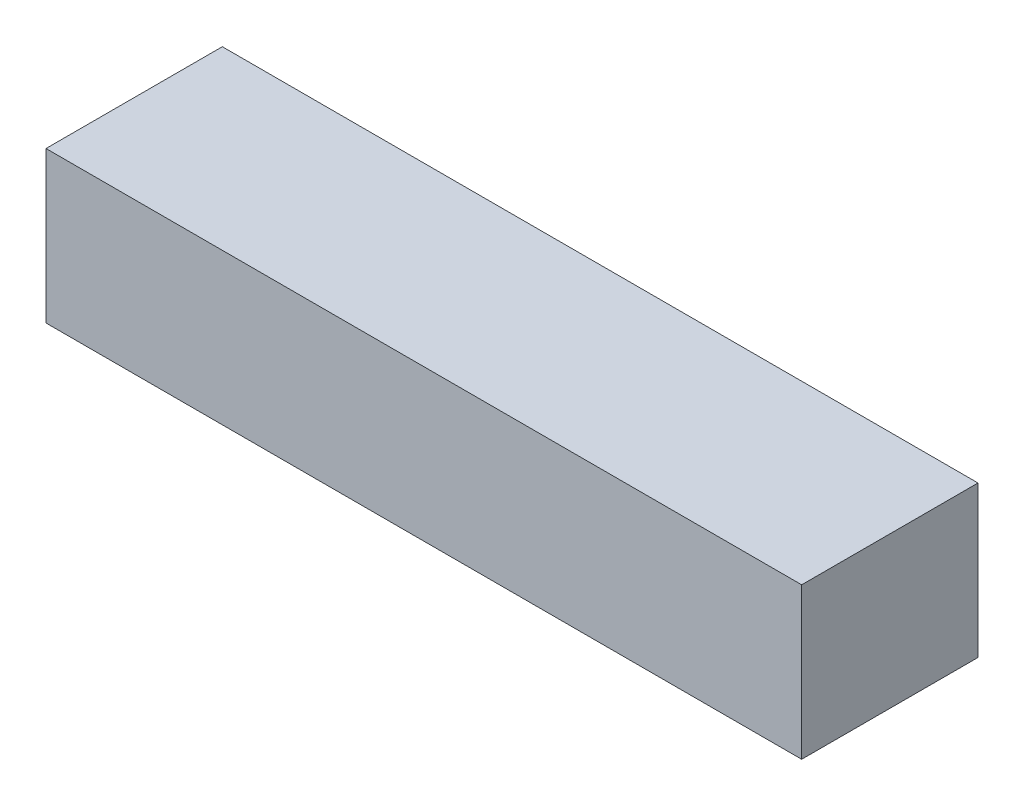
SolidWorks part; units mm, degrees
material "Maple"
ref_plane "Front Plane" through (0, 0, 0) normal (0, 0, 1) x (1, 0, 0)
ref_plane "Top Plane" through (0, 0, 0) normal (0, 1, 0) x (1, 0, 0)
ref_plane "Right Plane" through (0, 0, 0) normal (1, 0, 0) x (0, 0, -1)
sketch "Sketch1" plane through (0, 0, 0) normal (0, 1, 0) x (1, 0, 0)
  line L1 (0, 0) -> (30, 0)
  line L2 (0, 0) -> (0, 7)
  line L3 (0, 7) -> (30, 7)
  line L4 (30, 0) -> (30, 7)
  dimension "D1" = 30
  dimension "D2" = 7
extrude "Boss-Extrude1" add sketch "Sketch1" along normal blind 6
ref_plane "Plane1" through (0, 3, 0) normal (0, 1, 0) x (1, 0, 0)
